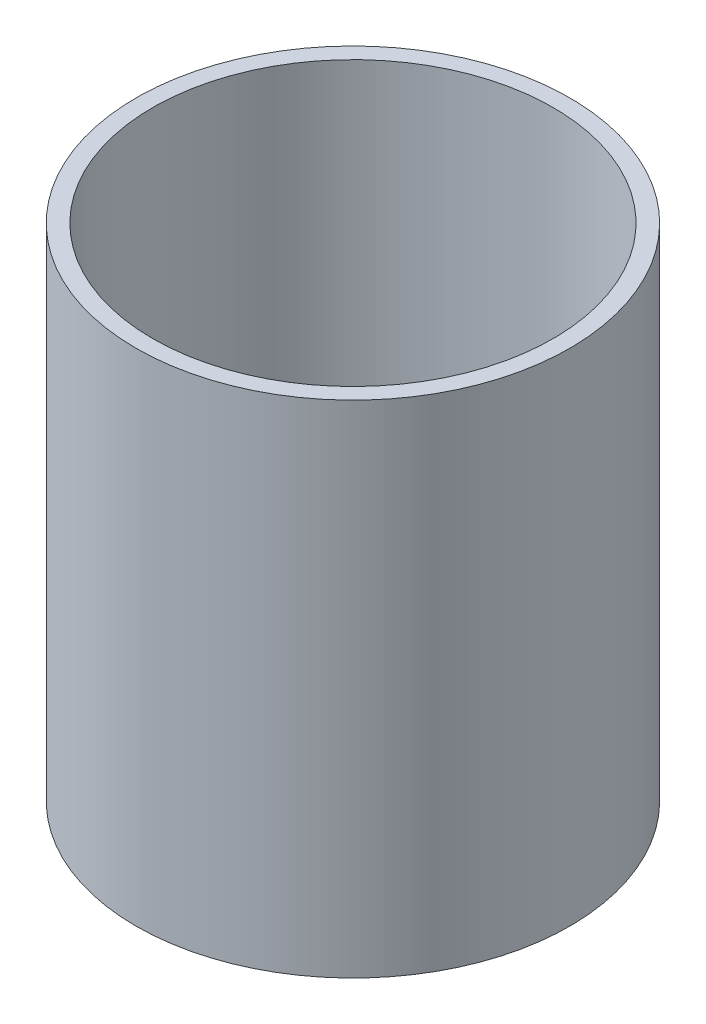
SolidWorks part; units mm, degrees
ref_plane "Front Plane" through (0, 0, 0) normal (0, 0, 1) x (1, 0, 0)
ref_plane "Top Plane" through (0, 0, 0) normal (0, 1, 0) x (1, 0, 0)
ref_plane "Right Plane" through (0, 0, 0) normal (1, 0, 0) x (0, 0, -1)
sketch "Sketch1" plane through (0, 0, 0) normal (0, 1, 0) x (1, 0, 0)
  circle A0 centre (0, 0) radius 24
  circle A1 centre (0, 0) radius 26
extrude "Boss-Extrude1" add sketch "Sketch1" along normal blind 60
